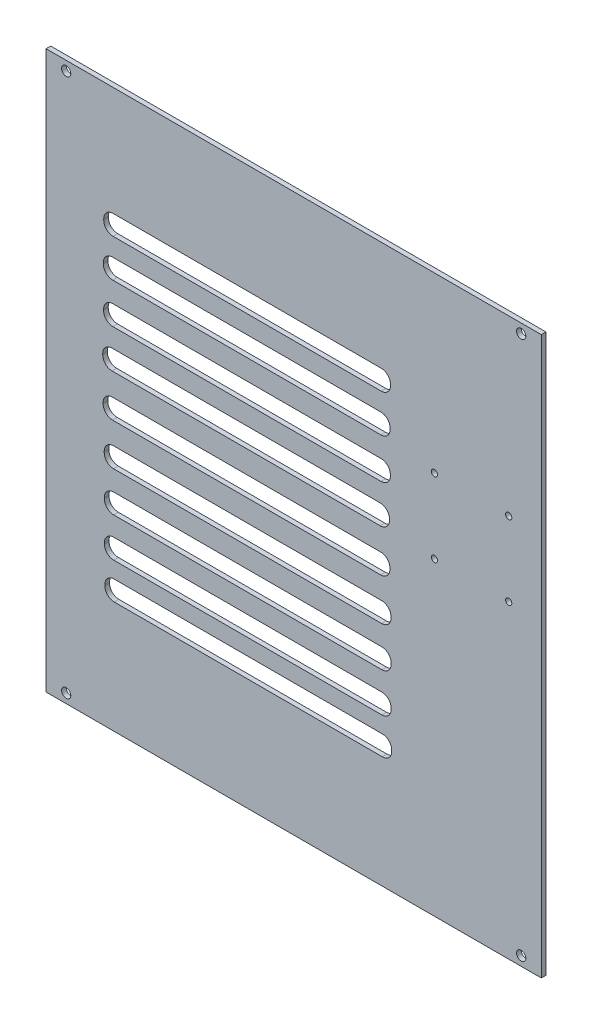
SolidWorks part; units mm, degrees
material "ABS PC"
ref_plane "前视基准面" through (0, 0, 0) normal (0, 0, 1) x (1, 0, 0)
ref_plane "上视基准面" through (0, 0, 0) normal (0, 1, 0) x (1, 0, 0)
ref_plane "右视基准面" through (0, 0, 0) normal (1, 0, 0) x (0, 0, -1)
sketch "草图1" plane through (0, 0, 0) normal (0, 0, 1) x (1, 0, 0)
  line L20 (1760.0473, 909.613) -> (1760.0473, -890.387)
  line L21 (1760.0473, -890.387) -> (3360.0473, -890.387)
  line L22 (3360.0473, -890.387) -> (3360.0473, 909.613)
  line L23 (3360.0473, 909.613) -> (1760.0473, 909.613)
  line L40 (1975.1021, 433.9431) -> (2841.4654, 433.9431)
  line L41 (1976.4528, 556.9981) -> (2842.816, 556.9981)
  line L42 (1946.4528, 526.9981) -> (1946.4528, 522.9816)
  line L43 (1976.4528, 492.9816) -> (2842.816, 492.9816)
  line L44 (2872.816, 526.9981) -> (2872.816, 522.9816)
  line L45 (1945.1021, 403.9431) -> (1945.1021, 399.9265)
  line L46 (1975.1021, 369.9265) -> (2841.4654, 369.9265)
  line L47 (2871.4654, 403.9431) -> (2871.4654, 399.9265)
  line L48 (1976.005, 304.0304) -> (2842.3683, 304.0304)
  line L49 (1946.005, 274.0304) -> (1946.005, 270.0138)
  line L50 (1976.005, 240.0138) -> (2842.3683, 240.0138)
  line L51 (2872.3683, 274.0304) -> (2872.3683, 270.0138)
  line L52 (1973.1457, 178.5975) -> (2839.5089, 178.5975)
  line L53 (1943.1457, 148.5975) -> (1943.1457, 144.5809)
  line L54 (1973.1457, 114.5809) -> (2839.5089, 114.5809)
  line L55 (2869.5089, 148.5975) -> (2869.5089, 144.5809)
  line L56 (1974.5498, 41.9651) -> (2840.913, 41.9651)
  line L57 (1944.5498, 11.9651) -> (1944.5498, 7.9486)
  line L58 (1974.5498, -22.0514) -> (2840.913, -22.0514)
  line L59 (2870.913, 11.9651) -> (2870.913, 7.9486)
  line L60 (1977.9908, -92.4273) -> (2844.354, -92.4273)
  line L61 (1947.9908, -122.4273) -> (1947.9908, -126.4438)
  line L62 (1977.9908, -156.4438) -> (2844.354, -156.4438)
  line L63 (2874.354, -122.4273) -> (2874.354, -126.4438)
  line L64 (1978.5444, -221.4963) -> (2844.9076, -221.4963)
  line L65 (1948.5444, -251.4963) -> (1948.5444, -255.5129)
  line L66 (1978.5444, -285.5129) -> (2844.9076, -285.5129)
  line L67 (2874.9076, -251.4963) -> (2874.9076, -255.5129)
  line L68 (1978.5792, -347.9372) -> (2844.9424, -347.9372)
  line L69 (1948.5792, -377.9372) -> (1948.5792, -381.9537)
  line L70 (1978.5792, -411.9537) -> (2844.9424, -411.9537)
  line L71 (2874.9424, -377.9372) -> (2874.9424, -381.9537)
  line L72 (1980.2377, -464.2464) -> (2846.6009, -464.2464)
  line L73 (1950.2377, -494.2464) -> (1950.2377, -498.2629)
  line L74 (1980.2377, -528.2629) -> (2846.6009, -528.2629)
  line L75 (2876.6009, -494.2464) -> (2876.6009, -498.2629)
  circle A44 centre (1825.0473, 879.613) radius 15
  circle A45 centre (1825.0473, -860.387) radius 15
  circle A46 centre (3295.0473, -860.387) radius 15
  circle A47 centre (3295.0473, 879.613) radius 15
  arc A64 (1976.4528, 556.9981) -> (1946.4528, 526.9981) centre (1976.4528, 526.9981) ccw
  arc A65 (1946.4528, 522.9816) -> (1976.4528, 492.9816) centre (1976.4528, 522.9816) ccw
  arc A66 (2842.816, 492.9816) -> (2872.816, 522.9816) centre (2842.816, 522.9816) ccw
  arc A67 (2842.816, 556.9981) -> (2872.816, 526.9981) centre (2842.816, 526.9981) cw
  arc A68 (1975.1021, 433.9431) -> (1945.1021, 403.9431) centre (1975.1021, 403.9431) ccw
  arc A69 (1945.1021, 399.9265) -> (1975.1021, 369.9265) centre (1975.1021, 399.9265) ccw
  arc A70 (2841.4654, 369.9265) -> (2871.4654, 399.9265) centre (2841.4654, 399.9265) ccw
  arc A71 (2841.4654, 433.9431) -> (2871.4654, 403.9431) centre (2841.4654, 403.9431) cw
  arc A72 (1976.005, 304.0304) -> (1946.005, 274.0304) centre (1976.005, 274.0304) ccw
  arc A73 (1946.005, 270.0138) -> (1976.005, 240.0138) centre (1976.005, 270.0138) ccw
  arc A74 (2842.3683, 240.0138) -> (2872.3683, 270.0138) centre (2842.3683, 270.0138) ccw
  arc A75 (2842.3683, 304.0304) -> (2872.3683, 274.0304) centre (2842.3683, 274.0304) cw
  arc A76 (1973.1457, 178.5975) -> (1943.1457, 148.5975) centre (1973.1457, 148.5975) ccw
  arc A77 (1943.1457, 144.5809) -> (1973.1457, 114.5809) centre (1973.1457, 144.5809) ccw
  arc A78 (2839.5089, 114.5809) -> (2869.5089, 144.5809) centre (2839.5089, 144.5809) ccw
  arc A79 (2839.5089, 178.5975) -> (2869.5089, 148.5975) centre (2839.5089, 148.5975) cw
  arc A80 (1974.5498, 41.9651) -> (1944.5498, 11.9651) centre (1974.5498, 11.9651) ccw
  arc A81 (1944.5498, 7.9486) -> (1974.5498, -22.0514) centre (1974.5498, 7.9486) ccw
  arc A82 (2840.913, -22.0514) -> (2870.913, 7.9486) centre (2840.913, 7.9486) ccw
  arc A83 (2840.913, 41.9651) -> (2870.913, 11.9651) centre (2840.913, 11.9651) cw
  arc A84 (1977.9908, -92.4273) -> (1947.9908, -122.4273) centre (1977.9908, -122.4273) ccw
  arc A85 (1947.9908, -126.4438) -> (1977.9908, -156.4438) centre (1977.9908, -126.4438) ccw
  arc A86 (2844.354, -156.4438) -> (2874.354, -126.4438) centre (2844.354, -126.4438) ccw
  arc A87 (2844.354, -92.4273) -> (2874.354, -122.4273) centre (2844.354, -122.4273) cw
  arc A88 (1978.5444, -221.4963) -> (1948.5444, -251.4963) centre (1978.5444, -251.4963) ccw
  arc A89 (1948.5444, -255.5129) -> (1978.5444, -285.5129) centre (1978.5444, -255.5129) ccw
  arc A90 (2844.9076, -285.5129) -> (2874.9076, -255.5129) centre (2844.9076, -255.5129) ccw
  arc A91 (2844.9076, -221.4963) -> (2874.9076, -251.4963) centre (2844.9076, -251.4963) cw
  arc A92 (1978.5792, -347.9372) -> (1948.5792, -377.9372) centre (1978.5792, -377.9372) ccw
  arc A93 (1948.5792, -381.9537) -> (1978.5792, -411.9537) centre (1978.5792, -381.9537) ccw
  arc A94 (2844.9424, -411.9537) -> (2874.9424, -381.9537) centre (2844.9424, -381.9537) ccw
  arc A95 (2844.9424, -347.9372) -> (2874.9424, -377.9372) centre (2844.9424, -377.9372) cw
  arc A96 (1980.2377, -464.2464) -> (1950.2377, -494.2464) centre (1980.2377, -494.2464) ccw
  arc A97 (1950.2377, -498.2629) -> (1980.2377, -528.2629) centre (1980.2377, -498.2629) ccw
  arc A98 (2846.6009, -528.2629) -> (2876.6009, -498.2629) centre (2846.6009, -498.2629) ccw
  arc A99 (2846.6009, -464.2464) -> (2876.6009, -494.2464) centre (2846.6009, -494.2464) cw
  circle A100 centre (3254.7079, 109.613) radius 10
  circle A101 centre (3014.7079, 109.613) radius 10
  circle A102 centre (3254.7079, 349.613) radius 10
  circle A103 centre (3014.7079, 349.613) radius 10
  dimension "D1" = 30
  dimension "D2" = 30
  dimension "D3" = 30
  dimension "D4" = 30
  dimension "D5" = 30
  dimension "D6" = 30
  dimension "D7" = 30
  dimension "D8" = 30
  dimension "D9" = 30
  dimension "D10" = 30
  dimension "D11" = 30
  dimension "D12" = 30
  dimension "D13" = 30
  dimension "D14" = 30
  dimension "D15" = 30
  dimension "D16" = 30
  dimension "D17" = 30
  dimension "D18" = 30
  dimension "D39" = 65
  dimension "D19" = 240
  dimension "D20" = 240
  dimension "D24" = 1600
  dimension "D38" = 30
extrude "凸台-拉伸1" add sketch "草图1" along normal blind 3
scale "缩放比例1" bodies to scale 101 104 102 103 108 scale about centroid uniform scaling no x scale factor 0.1 y scale factor 0.1 z scale factor 0.5
